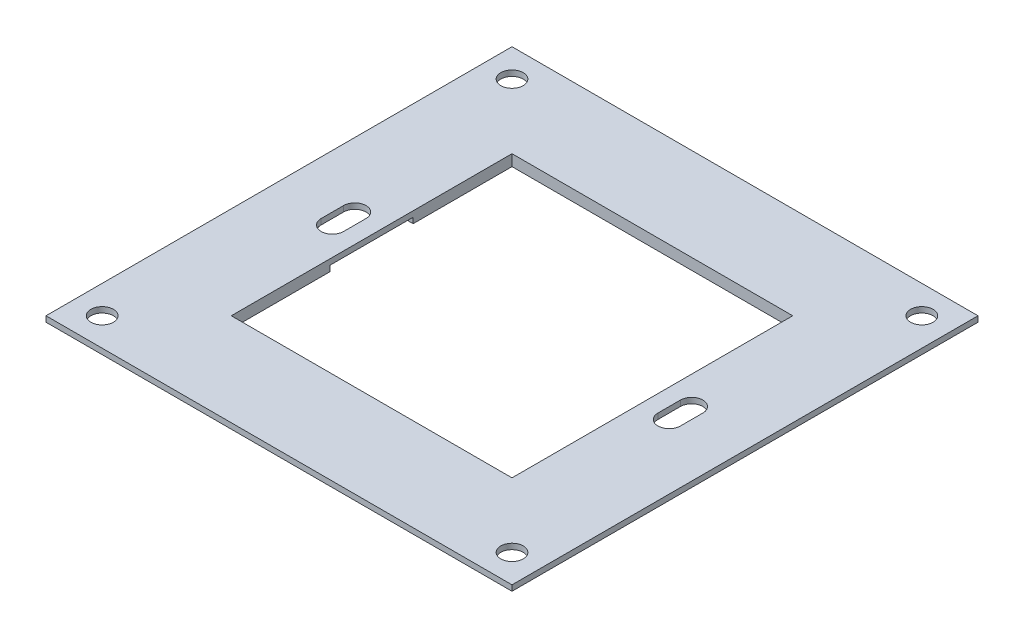
SolidWorks part; units mm, degrees
ref_plane "Спереди" through (0, 0, 0) normal (0, 0, 1) x (1, 0, 0)
ref_plane "Сверху" through (0, 0, 0) normal (0, 1, 0) x (1, 0, 0)
ref_plane "Справа" through (0, 0, 0) normal (1, 0, 0) x (0, 0, -1)
sketch "Эскиз1" plane through (0, 0, 0) normal (0, 1, 0) x (1, 0, 0)
  line L0 (28, 2) -> (28, -2)
  line L1 (-41.5, 41.5) -> (41.5, 41.5)
  line L2 (-41.5, 41.5) -> (-41.5, -41.5)
  line L3 (-41.5, -41.5) -> (41.5, -41.5)
  line L4 (41.5, 41.5) -> (41.5, -41.5)
  line L5 (-41.5, 41.5) -> (41.5, -41.5) construction
  line L6 (-41.5, -41.5) -> (41.5, 41.5) construction
  line L7 (-25, 25) -> (25, 25)
  line L8 (-25, 25) -> (-25, -25)
  line L9 (-25, -25) -> (25, -25)
  line L10 (25, 25) -> (25, -25)
  line L11 (-25, 25) -> (25, -25) construction
  line L12 (-25, -25) -> (25, 25) construction
  line L13 (32, 2) -> (32, -2)
  line L14 (0, 44.1785) -> (0, -47.9051) construction
  line L15 (-32, 2) -> (-32, -2)
  line L16 (-28, 2) -> (-28, -2)
  circle A0 centre (36.5, 36.5) radius 2
  circle A1 centre (-36.5, 36.5) radius 2
  circle A2 centre (-36.5, -36.5) radius 2
  circle A3 centre (36.5, -36.5) radius 2
  arc A4 (28, 2) -> (32, 2) centre (30, 2) cw
  arc A5 (28, -2) -> (32, -2) centre (30, -2) ccw
  arc A6 (-28, 2) -> (-32, 2) centre (-30, 2) ccw
  arc A7 (-28, -2) -> (-32, -2) centre (-30, -2) cw
  point P0 (0, 0)
  point P8 (0, 0)
  dimension "D1" = 2
  dimension "D2" = 2
extrude "Бобышка-Вытянуть1" add sketch "Эскиз1" along normal blind 1
sketch "Эскиз2" plane through (0, 0, 0) normal (0, 1, 0) x (1, 0, 0)
  line L0 (-25, -7.3931) -> (-34, -7.3931)
  line L1 (-25, 25) -> (-25, -25) construction
  line L2 (-34, -7.3931) -> (-34, -32)
  line L3 (-32, -34) -> (32, -34)
  line L4 (34, -32) -> (34, -7.3931)
  line L5 (34, -7.3931) -> (25, -7.3931)
  line L6 (25, -25) -> (25, 25) construction
  line L7 (25, -7.3931) -> (25, -25)
  line L8 (25, -25) -> (-25, -25)
  line L9 (-25, -25) -> (-25, -7.3931)
  line L10 (-47.2439, 0) -> (49.0472, 0) construction
  line L11 (-25, 25) -> (-25, 7.3931)
  line L12 (25, 25) -> (-25, 25)
  line L13 (25, 7.3931) -> (25, 25)
  line L14 (34, 7.3931) -> (25, 7.3931)
  line L15 (34, 32) -> (34, 7.3931)
  line L16 (-32, 34) -> (32, 34)
  line L17 (-34, 7.3931) -> (-34, 32)
  line L18 (-25, 7.3931) -> (-34, 7.3931)
  arc A0 (-34, -32) -> (-32, -34) centre (-32, -32) ccw
  arc A1 (32, -34) -> (34, -32) centre (32, -32) ccw
  arc A2 (34, 32) -> (32, 34) centre (32, 32) ccw
  arc A3 (-32, 34) -> (-34, 32) centre (-32, 32) ccw
  point P26 (0, 0)
  point P27 (0, 0)
  point P30 (-34, -34)
  point P33 (34, -34)
  point P36 (34, 34)
  point P39 (-34, 34)
  dimension "D1" = 2
extrude "Бобышка-Вытянуть2" add sketch "Эскиз2" against normal blind 1
